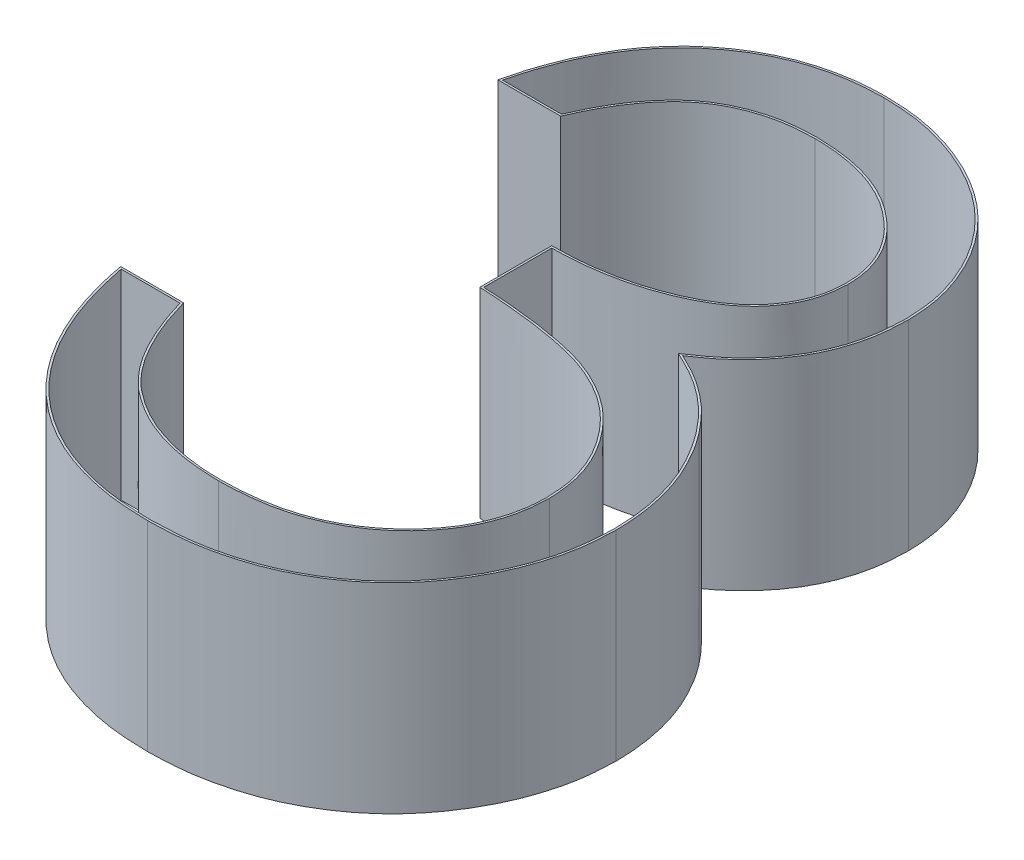
SolidWorks part; units mm, degrees
ref_plane "Front Plane" through (0, 0, 0) normal (0, 0, 1) x (1, 0, 0)
ref_plane "Top Plane" through (0, 0, 0) normal (0, 1, 0) x (1, 0, 0)
ref_plane "Right Plane" through (0, 0, 0) normal (1, 0, 0) x (0, 0, -1)
sketch "Sketch1" plane through (0, 0, 0) normal (0, 1, 0) x (1, 0, 0)
  text T0 "3"
extrude "Boss-Extrude1" add sketch "Sketch1" along normal blind 1
sketch "Sketch2" plane through (0, 1, 0) normal (0, 1, 0) x (1, 0, 0)
  line L9 (1.1318, 2.0991) -> (1.1318, 1.7595)
  line L10 (0.4413, 0.9323) -> (0.1468, 0.9323)
  line L11 (0.2819, 2.7023) -> (0.5768, 2.7023)
  line L12 (1.1318, 2.0991) -> (1.1318, 1.7595)
  line L13 (0.4413, 0.9323) -> (0.1468, 0.9323)
  line L14 (0.2819, 2.7023) -> (0.5768, 2.7023)
  spline S42 degree 3 poles (-3449.7273, 2026.015) (56.0672, -44.4765) (-2.8752, -2.2559) (0.738, 2.9842) (0.7916, 3.0476) (0.92, 3.1468) (0.995, 3.1835) (1.1119, 3.2186) (1.1523, 3.2275) (5.3717, 3.7672) (13.3888, -35.5491) (-369.6816, 3985.614) knots -19.055184 -19.055184 -19.055184 -19.055184 0.25 0.25 0.5 0.5 0.75 0.75 0.875 0.875 13.753556 13.753556 13.753556 13.753556 only from (0.5768, 2.7023) to (1.3152, 3.2408)
  spline S43 degree 3 poles (740.1225, 3934.219) (-28.2821, -81.766) (-4.8285, 4.9234) (1.6426, 3.1882) (1.7215, 3.1527) (1.8573, 3.054) (1.9189, 2.9943) (1.9849, 2.8858) (2.0012, 2.847) (3.1696, -1.3257) (-66.3805, -29.6343) (3148.3025, 2472.3909) knots -19.668822 -19.668822 -19.668822 -19.668822 0.25 0.25 0.5 0.5 0.75 0.75 0.875 0.875 13.72286 13.72286 13.72286 13.72286 only from (1.3152, 3.2408) to (2.0292, 2.6817)
  spline S44 degree 3 poles (3934.0507, -730.8163) (-64.0277, 22.9087) (3.2778, 6.2247) (1.9893, 2.4897) (1.9654, 2.4458) (1.8772, 2.3268) (1.793, 2.2676) (1.6165, 2.1808) (1.5225, 2.149) (1.3773, 2.1195) (1.3287, 2.1116) (-3.9469, 1.5581) (-14.4536, 44.6038) (466.5577, -3970.4705) knots -9.721659 -9.721659 -9.721659 -9.721659 0.125 0.125 0.25 0.25 0.5 0.5 0.75 0.75 0.875 0.875 14.215193 14.215193 14.215193 14.215193 only from (2.0292, 2.6817) to (1.1318, 2.0991)
  spline S45 degree 3 poles (424.5904, 3979.0973) (-25.7097, -66.2537) (-8.0509, 3.3982) (1.5568, 1.711) (1.617, 1.6986) (1.733, 1.6624) (1.789, 1.638) (1.8961, 1.577) (1.9453, 1.5412) (2.0332, 1.4564) (2.0725, 1.4082) (2.1383, 1.3056) (2.1649, 1.2493) (3.536, -3.308) (-65.5548, -20.7526) (3938.5, 710.3496) knots -19.543657 -19.543657 -19.543657 -19.543657 0.25 0.25 0.375 0.375 0.5 0.5 0.625 0.625 0.75 0.75 0.875 0.875 10.459825 10.459825 10.459825 10.459825 only from (1.1318, 1.7595) to (2.2087, 1.0097)
  spline S46 degree 3 poles (3945.8711, -666.8767) (-79.8345, 26.673) (3.5457, 6.4005) (2.1765, 0.7954) (2.1566, 0.7435) (2.0799, 0.6001) (2.0054, 0.5166) (1.8354, 0.3821) (1.7359, 0.3323) (-5.1886, -1.7085) (-38.3692, 86.6556) (1878.0534, -3531.9327) knots -13.034031 -13.034031 -13.034031 -13.034031 0.125 0.125 0.25 0.25 0.5 0.5 0.75 0.75 17.10918 17.10918 17.10918 17.10918 only from (2.2087, 1.0097) to (1.3076, 0.2592)
  spline S47 degree 3 poles (-1643.5583, -3645.7514) (39.1265, 99.1742) (8.2352, -1.9317) (0.9432, 0.3188) (0.8943, 0.3382) (-3.827, 2.8764) (20.013, 63.8693) (-1512.3322, -3702.0346) knots -35.174962 -35.174962 -35.174962 -35.174962 0.5 0.5 0.75 0.75 26.071263 26.071263 26.071263 26.071263 only from (1.3076, 0.2592) to (0.7165, 0.4508)
  spline S48 degree 3 poles (-2961.4799, -2687.226) (91.5327, 67.1679) (4.8696, -4.9445) (0.5906, 0.5904) (0.5663, 0.6302) (-2.82, 6.9759) (64.7069, 52.2758) (-3200.5463, -2397.4074) knots -36.552493 -36.552493 -36.552493 -36.552493 0.25 0.25 0.5 0.5 38.828187 38.828187 38.828187 38.828187 only from (0.7165, 0.4508) to (0.4413, 0.9323)
  spline S49 degree 3 poles (-3757.9024, -1368.4816) (100.3225, 58.0203) (-3.9119, 9.092) (0.3353, 0.4087) (0.418, 0.2911) (0.6278, 0.1028) (0.7507, 0.0306) (0.9524, -0.0375) (1.0207, -0.0543) (6.9952, -0.9571) (24.0387, 53.9011) (-977.5485, -3878.1448) knots -16.785623 -16.785623 -16.785623 -16.785623 0.25 0.25 0.5 0.5 0.75 0.75 0.875 0.875 11.485206 11.485206 11.485206 11.485206 only from (0.1468, 0.9323) to (1.302, -0.0797)
  spline S50 degree 3 poles (648.8215, -3946.9865) (-19.9552, 55.4915) (-4.3661, -1.0321) (1.6041, -0.0499) (1.6778, -0.0314) (1.8953, 0.045) (2.0287, 0.1238) (2.2536, 0.33) (2.3429, 0.4574) (2.4372, 0.6648) (2.4614, 0.7369) (3.7334, 6.3676) (-61.9724, 19.349) (3978.3833, -436.1862) knots -9.73707 -9.73707 -9.73707 -9.73707 0.125 0.125 0.25 0.25 0.5 0.5 0.75 0.75 0.875 0.875 10.132263 10.132263 10.132263 10.132263 only from (1.302, -0.0797) to (2.5028, 1.0398)
  spline S51 degree 3 poles (3990.6981, 304.8576) (-52.2733, -14.1392) (3.3469, -4.2007) (2.4812, 1.2599) (2.4683, 1.3136) (-0.2153, 9.3633) (-115.6502, -41.5379) (3592.6053, 1764.8216) knots -24.434774 -24.434774 -24.434774 -24.434774 0.25 0.25 0.5 0.5 38.514989 38.514989 38.514989 38.514989 only from (2.5028, 1.0398) to (2.296, 1.6556)
  spline S52 degree 3 poles (2844.3418, 2815.9739) (-20.6322, -31.4533) (5.1963, -1.3338) (2.2152, 1.7496) (2.1864, 1.7794) (2.155, 1.8067) (2.0893, 1.8575) (2.0545, 1.881) (2.0182, 1.9015) (-1.9011, 4.1098) (-22.2798, -23.9167) (1950.491, 3495.0749) knots -0.012743 -0.012743 -0.012743 -0.012743 0.000124 0.000124 0.000124 0.000248 0.000248 0.000374 0.000374 0.000374 0.013863 0.013863 0.013863 0.013863 only from (2.296, 1.6556) to (1.9047, 1.9588)
  spline S53 degree 3 poles (2511.5019, -3112.7665) (-43.3665, 42.1985) (-1.7146, -1.5806) (2.1301, 2.144) (2.1758, 2.2001) (2.2506, 2.3247) (2.279, 2.3931) (3.6521, 7.6623) (-65.1242, 33.4277) (3686.2346, -1555.0305) knots -17.763716 -17.763716 -17.763716 -17.763716 0.25 0.25 0.5 0.5 0.75 0.75 19.316819 19.316819 19.316819 19.316819 only from (1.9047, 1.9588) to (2.3233, 2.6803)
  spline S54 degree 3 poles (3929.9761, 758.737) (-58.6461, -19.0301) (3.4584, -1.8749) (2.2867, 2.926) (2.2642, 2.9856) (2.1814, 3.154) (2.1021, 3.2549) (1.9112, 3.4152) (1.7987, 3.4763) (1.6216, 3.5384) (1.5602, 3.5545) (-3.6549, 4.4294) (-15.1929, -48.9438) (453.5373, 3977.6277) knots -9.6962 -9.6962 -9.6962 -9.6962 0.125 0.125 0.25 0.25 0.5 0.5 0.75 0.75 0.875 0.875 11.29488 11.29488 11.29488 11.29488 only from (2.3233, 2.6803) to (1.311, 3.5797)
  spline S55 degree 3 poles (-630.0824, 3953.281) (23.2218, -57.991) (6.9548, 4.5471) (1.0677, 3.5549) (1.0081, 3.5404) (0.8334, 3.4774) (0.7291, 3.4141) (0.5424, 3.2519) (0.468, 3.1539) (-4.1, -5.2418) (105.5319, -57.898) (-3737.6186, 1425.9612) knots -11.97836 -11.97836 -11.97836 -11.97836 0.125 0.125 0.25 0.25 0.5 0.5 0.75 0.75 19.913874 19.913874 19.913874 19.913874 only from (1.311, 3.5797) to (0.2819, 2.7023)
  spline S56 degree 3 poles (0.5768, 2.7023) (0.6099, 2.7771) (0.6456, 2.8503) (0.738, 2.9842) (0.7916, 3.0476) (0.92, 3.1468) (0.995, 3.1835) (1.1119, 3.2186) (1.1523, 3.2275) (1.2334, 3.2379) (1.2743, 3.2393) (1.3152, 3.2408) knots 0 0 0 0 0.25 0.25 0.5 0.5 0.75 0.75 0.875 0.875 1 1 1 1
  spline S57 degree 3 poles (1.3152, 3.2408) (1.3992, 3.2388) (1.4821, 3.2312) (1.6426, 3.1882) (1.7215, 3.1527) (1.8573, 3.054) (1.9189, 2.9943) (1.9849, 2.8858) (2.0012, 2.847) (2.0237, 2.7666) (2.0283, 2.7241) (2.0292, 2.6817) knots 0 0 0 0 0.25 0.25 0.5 0.5 0.75 0.75 0.875 0.875 1 1 1 1
  spline S58 degree 3 poles (2.0292, 2.6817) (2.0267, 2.6322) (2.0216, 2.5833) (1.9893, 2.4897) (1.9654, 2.4458) (1.8772, 2.3268) (1.793, 2.2676) (1.6165, 2.1808) (1.5225, 2.149) (1.3773, 2.1195) (1.3287, 2.1116) (1.2307, 2.1013) (1.1813, 2.1) (1.1318, 2.0991) knots 0 0 0 0 0.125 0.125 0.25 0.25 0.5 0.5 0.75 0.75 0.875 0.875 1 1 1 1
  spline S59 degree 3 poles (1.1318, 1.7595) (1.254, 1.7526) (1.3759, 1.7428) (1.5568, 1.711) (1.617, 1.6986) (1.733, 1.6624) (1.789, 1.638) (1.8961, 1.577) (1.9453, 1.5412) (2.0332, 1.4564) (2.0725, 1.4082) (2.1383, 1.3056) (2.1649, 1.2493) (2.2002, 1.132) (2.2058, 1.0711) (2.2087, 1.0097) knots 0 0 0 0 0.25 0.25 0.375 0.375 0.5 0.5 0.625 0.625 0.75 0.75 0.875 0.875 1 1 1 1
  spline S60 degree 3 poles (2.2087, 1.0097) (2.2075, 0.955) (2.2023, 0.9009) (2.1765, 0.7954) (2.1566, 0.7435) (2.0799, 0.6001) (2.0054, 0.5166) (1.8354, 0.3821) (1.7359, 0.3323) (1.5275, 0.2709) (1.4171, 0.2613) (1.3076, 0.2592) knots 0 0 0 0 0.125 0.125 0.25 0.25 0.5 0.5 0.75 0.75 1 1 1 1
  spline S61 degree 3 poles (1.3076, 0.2592) (1.2016, 0.2608) (1.0955, 0.2718) (0.9432, 0.3188) (0.8943, 0.3382) (0.802, 0.3878) (0.7586, 0.4183) (0.7165, 0.4508) knots 0 0 0 0 0.5 0.5 0.75 0.75 1 1 1 1
  spline S62 degree 3 poles (0.7165, 0.4508) (0.681, 0.4819) (0.6484, 0.5157) (0.5906, 0.5904) (0.5663, 0.6302) (0.5004, 0.7535) (0.4686, 0.8424) (0.4413, 0.9323) knots 0 0 0 0 0.25 0.25 0.5 0.5 1 1 1 1
  spline S63 degree 3 poles (0.1468, 0.9323) (0.1744, 0.7941) (0.2125, 0.6598) (0.3353, 0.4087) (0.418, 0.2911) (0.6278, 0.1028) (0.7507, 0.0306) (0.9524, -0.0375) (1.0207, -0.0543) (1.1599, -0.0753) (1.231, -0.0781) (1.302, -0.0797) knots 0 0 0 0 0.25 0.25 0.5 0.5 0.75 0.75 0.875 0.875 1 1 1 1
  spline S64 degree 3 poles (1.302, -0.0797) (1.3784, -0.0775) (1.4547, -0.0745) (1.6041, -0.0499) (1.6778, -0.0314) (1.8953, 0.045) (2.0287, 0.1238) (2.2536, 0.33) (2.3429, 0.4574) (2.4372, 0.6648) (2.4614, 0.7369) (2.4953, 0.8869) (2.5, 0.9633) (2.5028, 1.0398) knots 0 0 0 0 0.125 0.125 0.25 0.25 0.5 0.5 0.75 0.75 0.875 0.875 1 1 1 1
  spline S65 degree 3 poles (2.5028, 1.0398) (2.5014, 1.0952) (2.4985, 1.1504) (2.4812, 1.2599) (2.4683, 1.3136) (2.4157, 1.4714) (2.3611, 1.5664) (2.296, 1.6556) knots 0 0 0 0 0.25 0.25 0.5 0.5 1 1 1 1
  spline S66 degree 3 poles (2.296, 1.6556) (2.27, 1.6877) (2.2439, 1.7199) (2.2152, 1.7496) (2.1864, 1.7794) (2.155, 1.8067) (2.0893, 1.8575) (2.0545, 1.881) (2.0182, 1.9015) (1.9813, 1.9223) (1.9429, 1.9404) (1.9047, 1.9588) knots 0 0 0 0 0.000124 0.000124 0.000124 0.000248 0.000248 0.000374 0.000374 0.000374 0.000501 0.000501 0.000501 0.000501
  spline S67 degree 3 poles (1.9047, 1.9588) (1.9649, 2.0002) (2.0248, 2.042) (2.1301, 2.144) (2.1758, 2.2001) (2.2506, 2.3247) (2.279, 2.3931) (2.3155, 2.5331) (2.321, 2.6069) (2.3233, 2.6803) knots 0 0 0 0 0.25 0.25 0.5 0.5 0.75 0.75 1 1 1 1
  spline S68 degree 3 poles (2.3233, 2.6803) (2.3206, 2.743) (2.3161, 2.8054) (2.2867, 2.926) (2.2642, 2.9856) (2.1814, 3.154) (2.1021, 3.2549) (1.9112, 3.4152) (1.7987, 3.4763) (1.6216, 3.5384) (1.5602, 3.5545) (1.4366, 3.5753) (1.3739, 3.5778) (1.311, 3.5797) knots 0 0 0 0 0.125 0.125 0.25 0.25 0.5 0.5 0.75 0.75 0.875 0.875 1 1 1 1
  spline S69 degree 3 poles (1.311, 3.5797) (1.2494, 3.5786) (1.1881, 3.5752) (1.0677, 3.5549) (1.0081, 3.5404) (0.8334, 3.4774) (0.7291, 3.4141) (0.5424, 3.2519) (0.468, 3.1539) (0.3503, 2.9377) (0.3109, 2.822) (0.2819, 2.7023) knots 0 0 0 0 0.125 0.125 0.25 0.25 0.5 0.5 0.75 0.75 1 1 1 1
  dimension "D1" = 0.01
extrude "Cut-Extrude1" cut sketch "Sketch2" against normal blind 1
